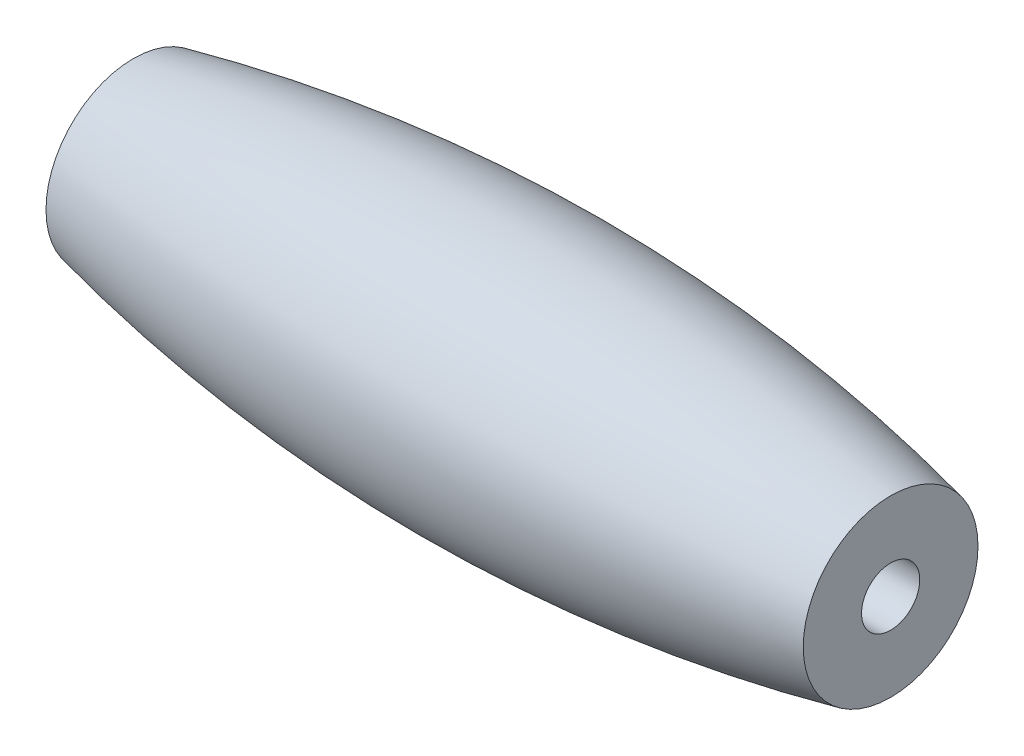
SolidWorks part; units mm, degrees
ref_plane "Front Plane" through (0, 0, 0) normal (0, 0, 1) x (1, 0, 0)
ref_plane "Top Plane" through (0, 0, 0) normal (0, 1, 0) x (1, 0, 0)
ref_plane "Right Plane" through (0, 0, 0) normal (1, 0, 0) x (0, 0, -1)
sketch "Sketch4" plane through (0, 0, 0) normal (0, 0, 1) x (1, 0, 0)
  line L0 (-6.5, 0) -> (-6.5, 1.5)
  line L1 (6.5, 1.5) -> (6.5, 0)
  line L3 (0, 0) -> (24465.105, 0) construction
  line L4 (-6.5, 0) -> (6.5, 0)
  arc A1 (-6.5, 1.5) -> (6.5, 1.5) centre (0, -27.7874) cw
  point P4 (-6.3609, 1.5)
  point P5 (-8.1446, 0)
  point P9 (0, 0)
  dimension "D3" = 30
  dimension "D1" = 3
  dimension "D2" = 13
revolve "Revolve1" add sketch "Sketch4" angle 360 about L3
sketch "Sketch8" plane through (0, 0, 0) normal (1, 0, 0) x (0, 0, -1)
  circle A0 centre (0, 0) radius 0.5
  dimension "D1" = 1
extrude "Cut-Extrude1" cut sketch "Sketch8" against normal through all both and the other way through all
